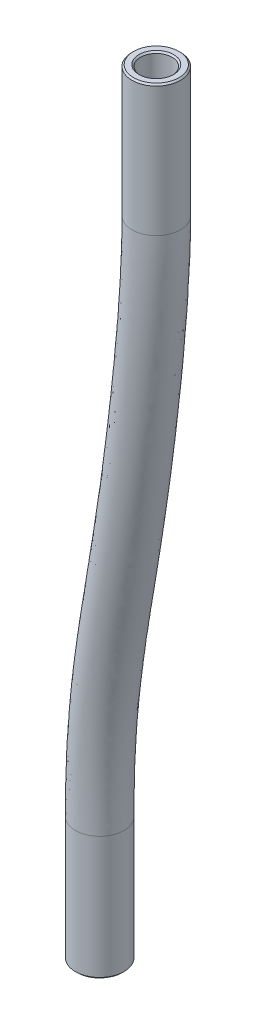
SolidWorks part; units mm, degrees
ref_plane "Front Plane" through (0, 0, 0) normal (0, 0, 1) x (1, 0, 0)
ref_plane "Top Plane" through (0, 0, 0) normal (0, 1, 0) x (1, 0, 0)
ref_plane "Right Plane" through (0, 0, 0) normal (1, 0, 0) x (0, 0, -1)
sketch3d "3DSketch1"
  line L0 (-150.0853, -93.2823, 25.525) -> (-150.0853, -103.4823, 25.525)
  line L1 (-143.9437, -35.8, 27.0016) -> (-143.9437, -46.6, 27.0016)
  spline S0 degree 3 poles (-143.9437, -46.6, 27.0016) (-143.9437, -51.7708, 27.0016) (-147.0145, -75.1317, 26.2633) (-150.0853, -82.5515, 25.525) (-150.0853, -93.2823, 25.525) knots 0 0 0 0 0.329296 1 1 1 1
sketch "Sketch1" plane through (0, -95.3823, 0) normal (0, 1, 0) x (1, 0, 0)
  circle A0 centre (-150.0853, -25.525) radius 2
  circle A1 centre (-150.0853, -25.525) radius 3.6 construction
  circle A2 centre (-150.0853, -25.525) radius 1.3
  dimension "D1" = 4
  dimension "D2" = 2.6
sweep "Sweep1" add profiles "Sketch1" path "3DSketch1"
chamfer "Chamfer1" distance 0.127 angle 45 4 edges at (-152.0853, -103.4823, 25.525) (-151.3853, -103.4823, 25.525) (-145.9437, -35.8, 27.0016) (-145.2437, -35.8, 27.0016)
